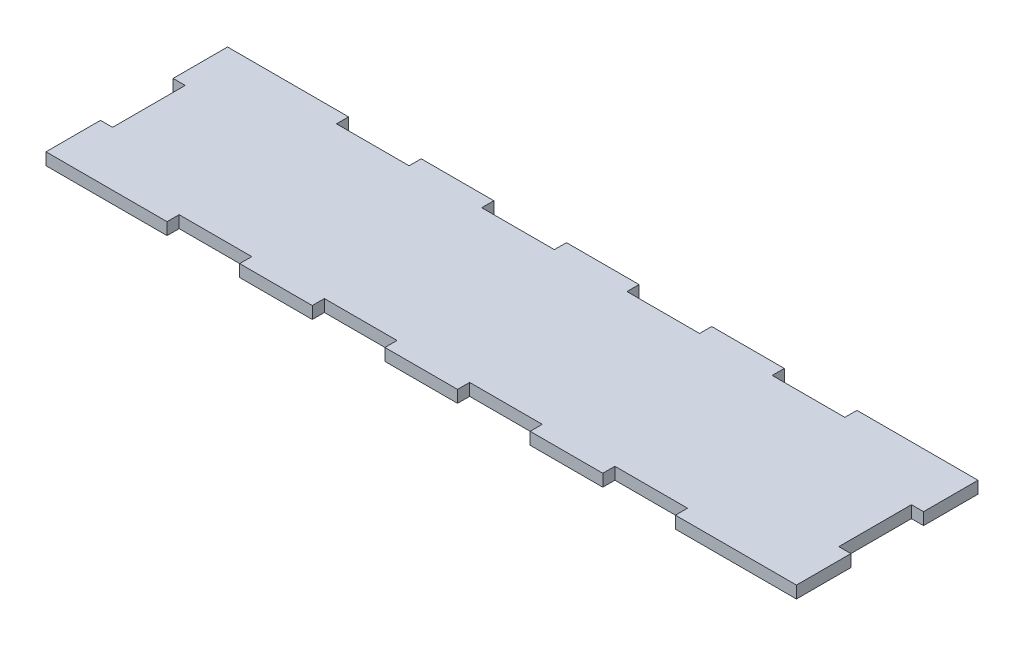
SolidWorks part; units mm, degrees
ref_plane "Plan de face" through (0, 0, 0) normal (0, 0, 1) x (1, 0, 0)
ref_plane "Plan de dessus" through (0, 0, 0) normal (0, 1, 0) x (1, 0, 0)
ref_plane "Plan de droite" through (0, 0, 0) normal (1, 0, 0) x (0, 0, -1)
sketch "Esquisse1" plane through (0, 0, 0) normal (0, 1, 0) x (1, 0, 0)
  line L1 (-196.85, 47.625) -> (196.85, 47.625)
  line L2 (-196.85, 47.625) -> (-196.85, -47.625)
  line L3 (-196.85, -47.625) -> (196.85, -47.625)
  line L4 (196.85, 47.625) -> (196.85, -47.625)
  point P4 (0, 47.625)
  point P6 (-196.85, 0)
  dimension "D1" = 393.7
  dimension "D2" = 95.25
extrude "Boss.-Extru.1" add sketch "Esquisse1" along normal blind 6.35
sketch "Esquisse2" plane through (-196.85, 0, 0) normal (-1, 0, 0) x (0, 0, 1)
  line L0 (-47.625, 6.35) -> (47.625, 6.35) construction
  line L1 (-19.05, 6.35) -> (19.05, 6.35)
  line L2 (-19.05, 6.35) -> (-19.05, 0)
  line L3 (-19.05, 0) -> (19.05, 0)
  line L4 (19.05, 6.35) -> (19.05, 0)
  line L5 (-47.625, 0) -> (47.625, 0) construction
  point P8 (0, 6.35)
  dimension "D1" = 38.1
extrude "Enlèv. mat.-Extru.1" cut sketch "Esquisse2" against normal blind 6.35
mirror "Symétrie1" about plane through (0, 0, 0) normal (1, 0, 0) of "Enlèv. mat.-Extru.1"
sketch "Esquisse3" plane through (0, 0, -47.625) normal (0, 0, -1) x (-1, 0, 0)
  line L0 (-196.85, 0) -> (196.85, 0) construction
  line L1 (133.35, 0) -> (95.25, 0)
  line L2 (133.35, 0) -> (133.35, 6.35)
  line L3 (133.35, 6.35) -> (95.25, 6.35)
  line L4 (95.25, 0) -> (95.25, 6.35)
  line L5 (-196.85, 6.35) -> (196.85, 6.35) construction
  line L6 (196.85, 6.35) -> (196.85, 0) construction
  dimension "D1" = 38.1
  dimension "D2" = 63.5
extrude "Enlèv. mat.-Extru.2" cut sketch "Esquisse3" against normal blind 6.35
pattern_linear "Répétition linéaire1" count 4 spacing 76.2 along (1, 0, 0) of "Enlèv. mat.-Extru.2"
mirror "Symétrie2" about plane through (0, 0, 0) normal (0, 0, 1) of "Répétition linéaire1", "Enlèv. mat.-Extru.2"
